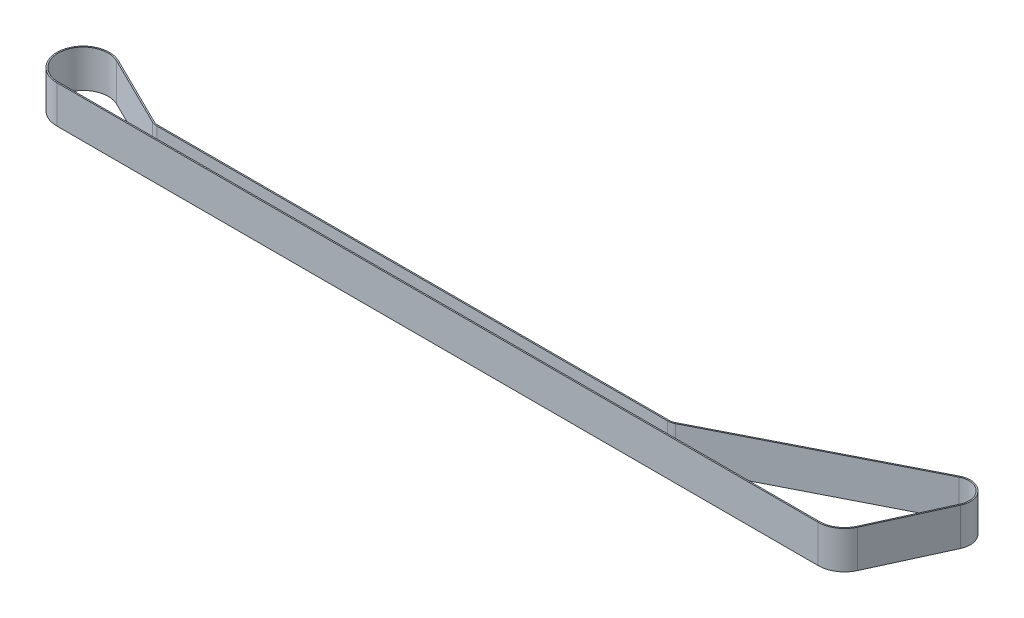
SolidWorks part; units mm, degrees
ref_plane "Front Plane" through (0, 0, 0) normal (0, 0, 1) x (1, 0, 0)
ref_plane "Top Plane" through (0, 0, 0) normal (0, 1, 0) x (1, 0, 0)
ref_plane "Right Plane" through (0, 0, 0) normal (1, 0, 0) x (0, 0, -1)
sketch "Sketch1" plane through (0, 0, 0) normal (0, 1, 0) x (1, 0, 0)
  line L0 (0, -10) -> (303.94, -10)
  line L1 (325.983, 24.0825) -> (313.0301, -4.1679)
  line L2 (241.3302, -4.904) -> (316.4507, 33.2414)
  line L3 (238.84, -5.5) -> (35, -5.5)
  line L4 (4.4286, 8.9659) -> (32.5643, -4.9313)
  line L5 (238.84, -5) -> (35, -5)
  line L6 (4.65, 9.4142) -> (32.7857, -4.483)
  line L7 (0, -10.5) -> (303.94, -10.5)
  line L8 (326.4375, 23.8741) -> (313.4846, -4.3762)
  line L9 (241.1038, -4.4582) -> (316.2243, 33.6872)
  circle A0 centre (0, 0) radius 10 construction
  circle A1 centre (35, 0) radius 5.5 construction
  circle A2 centre (238.84, 0) radius 5.5 construction
  circle A3 centre (303.94, 0) radius 10 construction
  circle A4 centre (319.62, 27) radius 7 construction
  arc A5 (4.4286, 8.9659) -> (0, -10) centre (0, 0) ccw
  arc A6 (32.5643, -4.9313) -> (35, -5.5) centre (35, 0) ccw
  arc A7 (238.84, -5.5) -> (241.3302, -4.904) centre (238.84, 0) ccw
  arc A8 (325.983, 24.0825) -> (316.4507, 33.2414) centre (319.62, 27) ccw
  arc A9 (303.94, -10) -> (313.0301, -4.1679) centre (303.94, 0) ccw
  arc A10 (32.7857, -4.483) -> (35, -5) centre (35, 0) ccw
  arc A11 (4.65, 9.4142) -> (0, -10.5) centre (0, 0) ccw
  arc A12 (303.94, -10.5) -> (313.4846, -4.3762) centre (303.94, 0) ccw
  arc A13 (326.4375, 23.8741) -> (316.2243, 33.6872) centre (319.62, 27) ccw
  arc A14 (238.84, -5) -> (241.1038, -4.4582) centre (238.84, 0) ccw
  dimension "D1" = 20
  dimension "D2" = 11
  dimension "D3" = 11
  dimension "D4" = 20
  dimension "D8" = 14
  dimension "D5" = 35
  dimension "D6" = 203.84
  dimension "D7" = 65.1
  dimension "D9" = 27
  dimension "D10" = 15.68
  dimension "D11" = 0.5
extrude "Boss-Extrude1" add sketch "Sketch1" along normal blind 15
